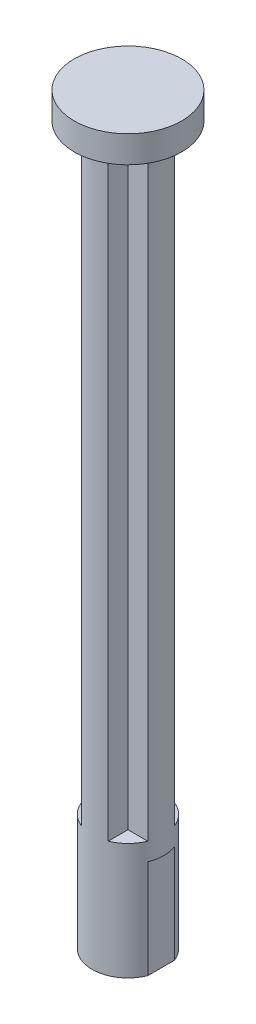
SolidWorks part; units mm, degrees
ref_plane "Front Plane" through (0, 0, 0) normal (0, 0, 1) x (1, 0, 0)
ref_plane "Top Plane" through (0, 0, 0) normal (0, 1, 0) x (1, 0, 0)
ref_plane "Right Plane" through (0, 0, 0) normal (1, 0, 0) x (0, 0, -1)
sketch "Sketch4" plane through (0, 0, 0) normal (0, 1, 0) x (1, 0, 0)
  circle A0 centre (0, 0) radius 4
  dimension "D1" = 8
extrude "Boss-Extrude6" add sketch "Sketch4" along normal blind 13
sketch "Sketch5" plane through (0, 0, 0) normal (0, -1, 0) x (1, 0, 0)
  line L3 (-3.7081, -1.5) -> (-3.7081, 1.5)
  line L4 (3.7081, -1.5) -> (3.7081, 1.5)
  circle A1 centre (0, 0) radius 4 construction
  arc A2 (3.7081, -1.5) -> (3.7081, 1.5) centre (0, 0) ccw
  circle A3 centre (0, 0) radius 4
  arc A4 (-3.7081, 1.5) -> (-3.7081, -1.5) centre (0, 0) ccw
  point P3 (0, 0)
  point P10 (0, 0)
  point P11 (0, 0)
  point P13 (0, 0)
  point P14 (0, 0)
  point P15 (0, 0)
  point P16 (0, 0)
  dimension "D3" = 0
extrude "Cut-Extrude3" cut sketch "Sketch5" against normal blind 11 and the other way through all
sketch "Sketch6" plane through (-3.7081, 0, 0) normal (-1, 0, 0) x (0, 0, 1)
  circle A0 centre (0, 5) radius 1.5
  dimension "D1" = 5
  dimension "D2" = 3
extrude "Cut-Extrude4" cut sketch "Sketch6" against normal blind 3
sketch "Sketch7" plane through (0, 13, 0) normal (0, 1, 0) x (1, 0, 0)
  line L0 (1.5, 1.5) -> (1.5, 3.7081)
  line L1 (-1.5, 1.5) -> (-3.7081, 1.5)
  line L2 (-1.5, -1.5) -> (-3.7081, -1.5)
  line L5 (-1.5, 1.5) -> (-1.5, 3.7081)
  line L6 (1.5, -1.5) -> (3.7081, -1.5)
  line L7 (1.5, 1.5) -> (3.7081, 1.5)
  line L8 (-1.5, -1.5) -> (-1.5, -3.7081)
  line L9 (1.5, -1.5) -> (1.5, -3.7081)
  arc A1 (1.5, 3.7081) -> (-1.5, 3.7081) centre (0, 0) ccw
  circle A2 centre (0, 0) radius 4
  arc A3 (-3.7081, 1.5) -> (-3.7081, -1.5) centre (0, 0) ccw
  arc A4 (3.7081, -1.5) -> (3.7081, 1.5) centre (0, 0) ccw
  arc A5 (-1.5, -3.7081) -> (1.5, -3.7081) centre (0, 0) ccw
  point P23 (0, 0)
  dimension "D1" = 4
  dimension "D3" = 0
extrude "Boss-Extrude7" add sketch "Sketch7" along normal blind 67
sketch "Sketch8" plane through (0, 80, 0) normal (0, 1, 0) x (1, 0, 0)
  circle A0 centre (0, 0) radius 6
  dimension "D1" = 12
extrude "Boss-Extrude8" add sketch "Sketch8" along normal blind 3
sketch "Sketch9" plane through (3.7081, 0, 0) normal (1, 0, 0) x (0, 0, -1)
  line L0 (1.5, 0) -> (-1.5, 0) construction
  circle A0 centre (0, 5) radius 1.5
  dimension "D1" = 5
  dimension "D2" = 3
